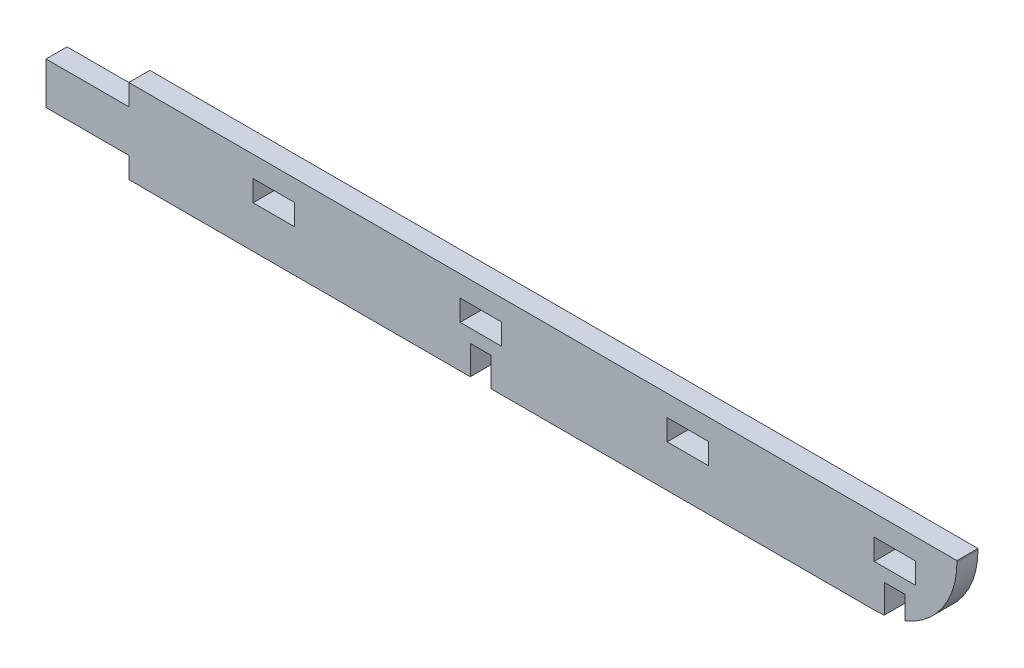
SolidWorks part; units mm, degrees
ref_plane "Front Plane" through (0, 0, 0) normal (0, 0, 1) x (1, 0, 0)
ref_plane "Top Plane" through (0, 0, 0) normal (0, 1, 0) x (1, 0, 0)
ref_plane "Right Plane" through (0, 0, 0) normal (1, 0, 0) x (0, 0, -1)
sketch "Sketch1" plane through (0, 0, 0) normal (0, 0, 1) x (1, 0, 0)
  line L0 (-100, 5.08) -> (-100, 10.16)
  line L1 (-100, -10.16) -> (100, -10.16)
  line L2 (-100, -10.16) -> (-100, -5.08)
  line L3 (-100, 10.16) -> (100, 10.16)
  line L4 (100, -10.16) -> (100, 10.16)
  line L5 (-100, -10.16) -> (100, 10.16) construction
  line L6 (-100, 10.16) -> (100, -10.16) construction
  line L7 (-100, 5.08) -> (-120, 5.08)
  line L8 (-100, 5.08) -> (-100, -5.08) construction
  line L9 (-100, -5.08) -> (-120, -5.08)
  line L10 (-120, 5.08) -> (-120, -5.08)
  point P0 (0, 0)
  point P10 (-100, 0)
  dimension "D1" = 200
  dimension "D2" = 20.32
  dimension "D3" = 10.16
  dimension "D4" = 20
extrude "Boss-Extrude1" add sketch "Sketch1" along normal blind 5.08
fillet "Fillet1" radius 20 1 edges at (100, -10.16, 2.54)
sketch "Sketch2" plane through (0, 0, 5.08) normal (0, 0, 1) x (1, 0, 0)
  line L0 (-100, -10.16) -> (80, -10.16) construction
  line L1 (-17.54, -10.16) -> (-12.54, -10.16)
  line L2 (-17.54, -10.16) -> (-17.54, -3.16)
  line L3 (-17.54, -3.16) -> (-12.54, -3.16)
  line L4 (-12.54, -10.16) -> (-12.54, -3.16)
  line L5 (-100, 10.16) -> (-100, 5.08) construction
  line L6 (82.46, -10.16) -> (87.46, -10.16)
  line L7 (82.46, -10.16) -> (82.46, -3.16)
  line L8 (82.46, -3.16) -> (87.46, -3.16)
  line L9 (87.46, -10.16) -> (87.46, -3.16)
  line L10 (0, 0) -> (94.3827, 0) construction
  line L11 (-70, 5.08) -> (-60, 5.08)
  line L12 (-70, 5.08) -> (-70, 0)
  line L13 (-70, 0) -> (-60, 0)
  line L14 (-60, 5.08) -> (-60, 0)
  line L15 (-20, 5.08) -> (-10, 5.08)
  line L16 (-20, 5.08) -> (-20, 0)
  line L17 (-20, 0) -> (-10, 0)
  line L18 (-10, 5.08) -> (-10, 0)
  line L19 (30, 5.08) -> (40, 5.08)
  line L20 (30, 5.08) -> (30, 0)
  line L21 (30, 0) -> (40, 0)
  line L22 (40, 5.08) -> (40, 0)
  line L23 (80, 5.08) -> (90, 5.08)
  line L24 (80, 5.08) -> (80, 0)
  line L25 (80, 0) -> (90, 0)
  line L26 (90, 5.08) -> (90, 0)
  dimension "D1" = 82.46
  dimension "D2" = 5
  dimension "D3" = 7
  dimension "D4" = 95
  dimension "D5" = 10
  dimension "D6" = 5.08
  dimension "D7" = 30
  dimension "D9" = 40
  dimension "D8" = 4
extrude "Cut-Extrude1" cut sketch "Sketch2" against normal through all
